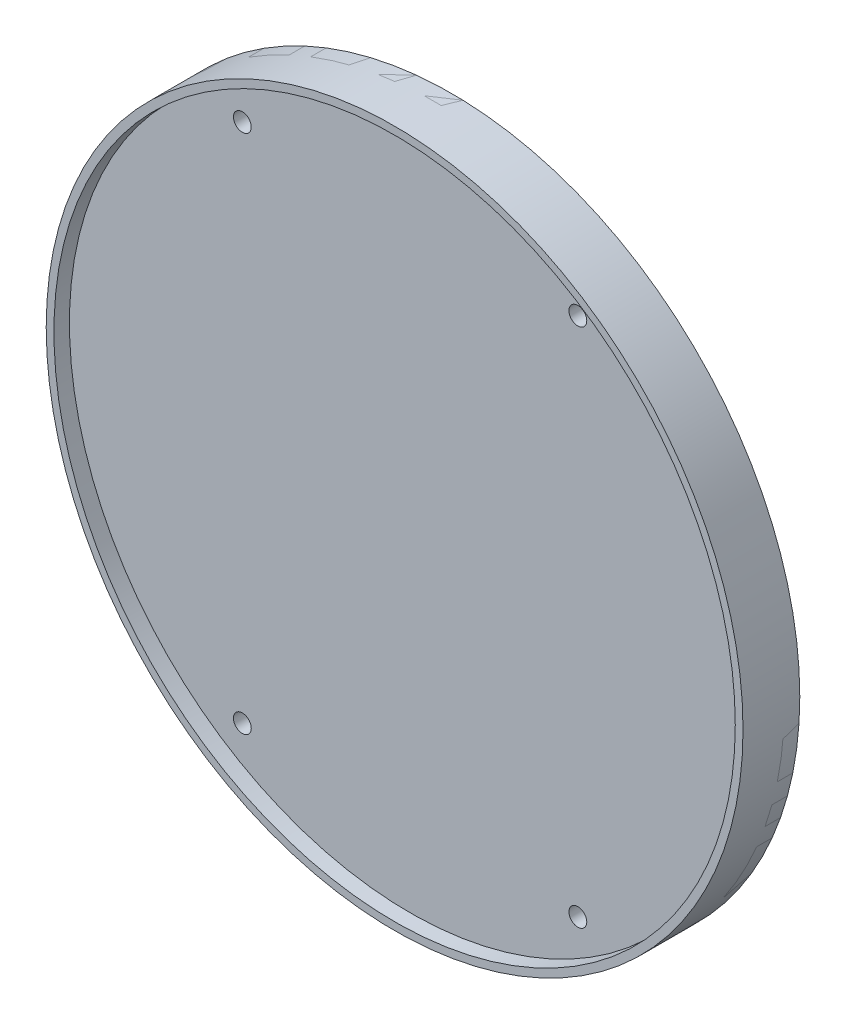
SolidWorks part; units mm, degrees
material "ABS"
ref_plane "Front Plane" through (0, 0, 0) normal (0, 0, 1) x (1, 0, 0)
ref_plane "Top Plane" through (0, 0, 0) normal (0, 1, 0) x (1, 0, 0)
ref_plane "Right Plane" through (0, 0, 0) normal (1, 0, 0) x (0, 0, -1)
sketch "Sketch2" plane through (0, 0, 0) normal (0, 0, 1) x (1, 0, 0)
  circle A1 centre (0, 0) radius 67.5
  circle A6 centre (-32.5, 50.4356) radius 2.5273
  circle A7 centre (-32.5, -50.4356) radius 2.5273
  circle A8 centre (32.5, -50.4356) radius 2.5273
  circle A9 centre (32.5, 50.4356) radius 2.5273
  circle A11 centre (0, 0) radius 66
  dimension "D1" = 135
  dimension "D2" = 132
extrude "Boss-Extrude2" add sketch "Sketch2" along normal blind 11 contours A1
sketch "Sketch3" plane through (0, 0, 0) normal (0, 0, -1) x (-1, 0, 0)
  circle A0 centre (0, 0) radius 66 construction
  circle A1 centre (0, 0) radius 66
extrude "Cut-Extrude11" cut sketch "Sketch3" against normal blind 3
sketch "Sketch15" plane through (0, 0, 11) normal (0, 0, 1) x (1, 0, 0)
  circle A0 centre (0, 0) radius 67.5 construction
  circle A1 centre (0, 0) radius 66
  dimension "D1" = 132
  dimension "D2" = 135
extrude "Cut-Extrude14" cut sketch "Sketch15" against normal blind 3
sketch "Sketch5" plane through (0, 0, 11) normal (0, 0, 1) x (1, 0, 0)
  circle A0 centre (0, 0) radius 66 construction
  circle A1 centre (0, 0) radius 66
sketch "Sketch28" plane through (0, 0, 3) normal (0, 0, -1) x (-1, 0, 0)
  circle A0 centre (0, 0) radius 67.5 construction
  circle A1 centre (0, 0) radius 67.5
extrude "Boss-Extrude14" add sketch "Sketch28" along normal blind 3 separate body
hole_wizard "CSK for #5 Flat Head Socket Cap Screw5" positions "3DSketch8" profile "Sketch30" countersink size "#5" standard "ANSI Inch"
sketch3d "3DSketch8"
  point P0 (32.5, 50.4356, 0)
  point P4 (-32.5, 50.4356, 0)
  point P8 (-32.5, -50.4356, 0)
  point P12 (32.5, -50.4356, 0)
sketch "Sketch30" plane through (32.5, 50.4356, 0) normal (1, 0, 0) x (0, 1, 0)
  line L0 (0, 0) -> (0, 69.3778)
  line L1 (0, 69.3778) -> (1.7272, 68.34)
  line L2 (1.7272, 68.34) -> (1.7272, 2.1184)
  line L3 (1.7272, 2.1184) -> (3.5687, 0)
  line L5 (3.5687, 0) -> (0, 0)
  line L6 (-1.7272, 2.1184) -> (-3.5687, 0) construction
  line L10 (0, 69.3778) -> (-1.7272, 68.34) construction
  line L11 (0, -6.35) -> (0, 107.95) construction
  dimension "Hole Dia." = 3.4544
  dimension "Hole Depth" = 68.34
  dimension "Near C'Sink Dia." = 7.1374
  dimension "Near C'Sink Angle" = 82
  dimension "Drill Angle" = 118
sketch "Sketch31" plane through (0, 0, 8) normal (0, 0, 1) x (1, 0, 0)
  line L0 (-66, 0) -> (66, 0) construction
  line L1 (0, 66) -> (0, -66) construction
  line L2 (-37.7, 13.5) -> (-2, 13.5) construction
  line L3 (-37.7, 44.6) -> (-2, 44.6) construction
  line L4 (-37.7, 44.6) -> (-37.7, 9) construction
  line L5 (-37.7, 9) -> (-2, 9) construction
  line L7 (-37.7, 40.1) -> (-2, 40.1) construction
  line L8 (37.7, 9) -> (2, 44.6) construction
  line L9 (37.7, 44.6) -> (2, 9) construction
  line L10 (-2, 44.6) -> (-2, 9) construction
  line L11 (-37.7, 44.6) -> (-2, 9) construction
  line L12 (-37.7, 9) -> (-2, 44.6) construction
  line L13 (2, 44.6) -> (2, 9) construction
  line L14 (37.7, 40.1) -> (2, 40.1) construction
  line L15 (37.7, 9) -> (2, 9) construction
  line L16 (37.7, 44.6) -> (37.7, 9) construction
  line L17 (37.7, 44.6) -> (2, 44.6) construction
  line L18 (37.7, 13.5) -> (2, 13.5) construction
  line L19 (37.7, -13.5) -> (2, -13.5) construction
  line L20 (37.7, -44.6) -> (2, -44.6) construction
  line L21 (37.7, -44.6) -> (37.7, -9) construction
  line L22 (37.7, -9) -> (2, -9) construction
  line L23 (37.7, -40.1) -> (2, -40.1) construction
  line L24 (2, -44.6) -> (2, -9) construction
  line L25 (37.7, -44.6) -> (2, -9) construction
  line L26 (37.7, -9) -> (2, -44.6) construction
  line L27 (-37.6, -1) -> (-37.6, -51.6) construction
  line L28 (-37.6, -51.6) -> (-2, -51.6) construction
  line L29 (-2, -51.6) -> (-2, -1) construction
  line L30 (-2, -1) -> (-37.6, -1) construction
  circle A0 centre (0, 0) radius 66 construction
  point P11 (-19.85, 26.8)
  point P26 (19.85, 26.8)
  point P35 (19.85, -26.8)
  dimension "D1" = 2
  dimension "D2" = 35.6
  dimension "D3" = 35.7
  dimension "D4" = 4.5
  dimension "D5" = 9
  dimension "D6" = 4.5
  dimension "D7" = 2
  dimension "D8" = 35.6
  dimension "D9" = 50.6
  dimension "D10" = 1
